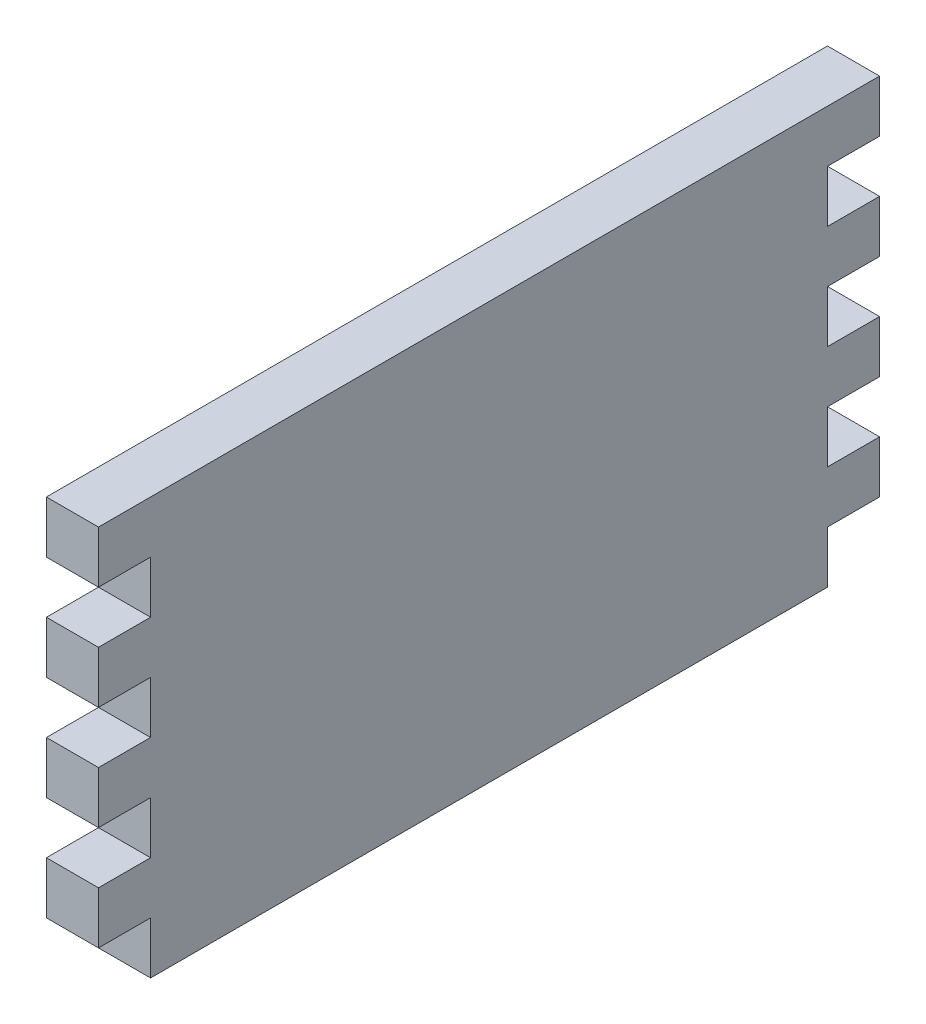
SolidWorks part; units mm, degrees
ref_plane "Plan de face" through (0, 0, 0) normal (0, 0, 1) x (1, 0, 0)
ref_plane "Plan de dessus" through (0, 0, 0) normal (0, 1, 0) x (1, 0, 0)
ref_plane "Plan de droite" through (0, 0, 0) normal (1, 0, 0) x (0, 0, -1)
sketch "Esquisse1" plane through (0, 0, 0) normal (1, 0, 0) x (0, 0, -1)
  line L1 (0, 0) -> (-150, 0)
  line L2 (0, 0) -> (0, 80)
  line L3 (0, 80) -> (-150, 80)
  line L4 (-150, 0) -> (-150, 80)
  dimension "D1" = 150
  dimension "D2" = 80
extrude "Boss.-Extru.1" add sketch "Esquisse1" along normal blind 10
sketch "Esquisse2" plane through (0, 0, 0) normal (-1, 0, 0) x (0, 0, 1)
  line L0 (0, 0) -> (0, 80) construction
  line L1 (0, 70) -> (10, 70)
  line L2 (0, 70) -> (0, 60)
  line L3 (0, 60) -> (10, 60)
  line L4 (10, 70) -> (10, 60)
  line L5 (150, 80) -> (150, 0) construction
  line L6 (150, 70) -> (140, 70)
  line L7 (150, 70) -> (150, 60)
  line L8 (150, 60) -> (140, 60)
  line L9 (140, 70) -> (140, 60)
  line L10 (0, 80) -> (150, 80) construction
  dimension "D1" = 10
  dimension "D2" = 10
  dimension "D3" = 10
  dimension "D4" = 10
  dimension "D5" = 10
  dimension "D6" = 10
extrude "Enlèv. mat.-Extru.1" cut sketch "Esquisse2" against normal blind 10
pattern_linear "Répétition linéaire1" count 4 spacing 20 along (0, -1, 0) of "Enlèv. mat.-Extru.1"
